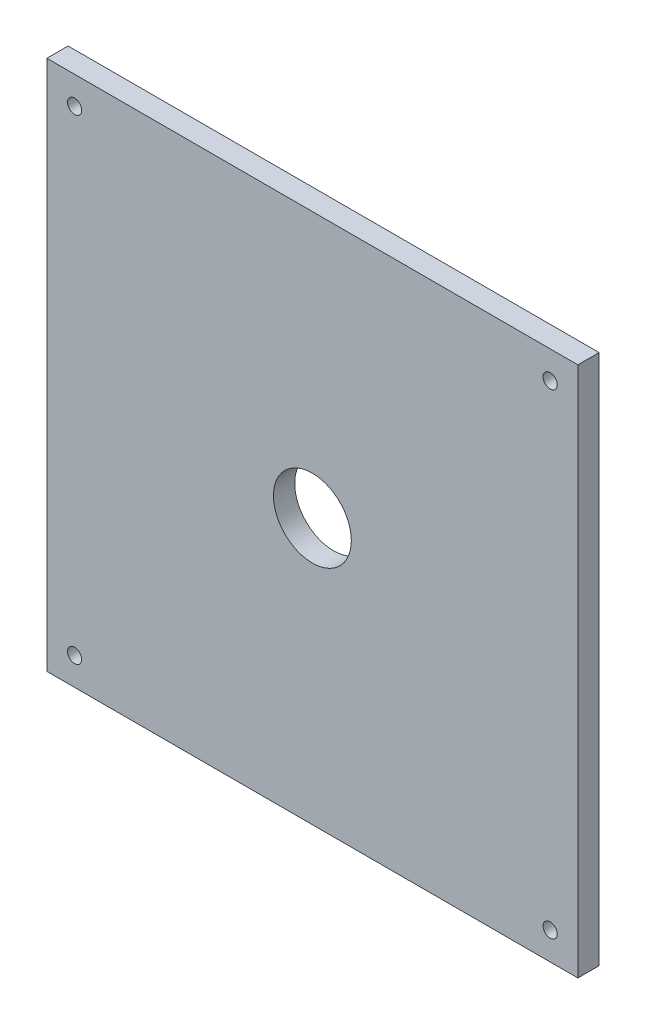
SolidWorks part; units mm, degrees
ref_plane "Front Plane" through (0, 0, 0) normal (0, 0, 1) x (1, 0, 0)
ref_plane "Top Plane" through (0, 0, 0) normal (0, 1, 0) x (1, 0, 0)
ref_plane "Right Plane" through (0, 0, 0) normal (1, 0, 0) x (0, 0, -1)
sketch "Sketch1" plane through (0, 0, 0) normal (0, 0, 1) x (1, 0, 0)
  line L1 (-75, -75) -> (75, -75)
  line L2 (-75, -75) -> (-75, 75)
  line L3 (-75, 75) -> (75, 75)
  line L4 (75, -75) -> (75, 75)
  line L5 (-75, -75) -> (75, 75) construction
  line L6 (-75, 75) -> (75, -75) construction
  circle A1 centre (0, 0) radius 11
  point P0 (0, 0)
  dimension "D4" = 22
  dimension "D1" = 150
  dimension "D2" = 150
extrude "Boss-Extrude1" add sketch "Sketch1" along normal blind 6
sketch "Sketch2" plane through (0, 0, 6) normal (0, 0, 1) x (1, 0, 0)
  line L0 (75, 75) -> (-75, -75) construction
  line L1 (-75, 75) -> (75, -75) construction
  circle A0 centre (67.1751, 67.1751) radius 2
  circle A1 centre (67.1751, -67.1751) radius 2
  circle A2 centre (-67.1751, -67.1751) radius 2
  circle A3 centre (-67.1751, 67.1751) radius 2
  point P20 (0, 0)
  dimension "D1" = 4
  dimension "D2" = 95
  dimension "D3" = 4
extrude "Cut-Extrude1" cut sketch "Sketch2" against normal blind 10
